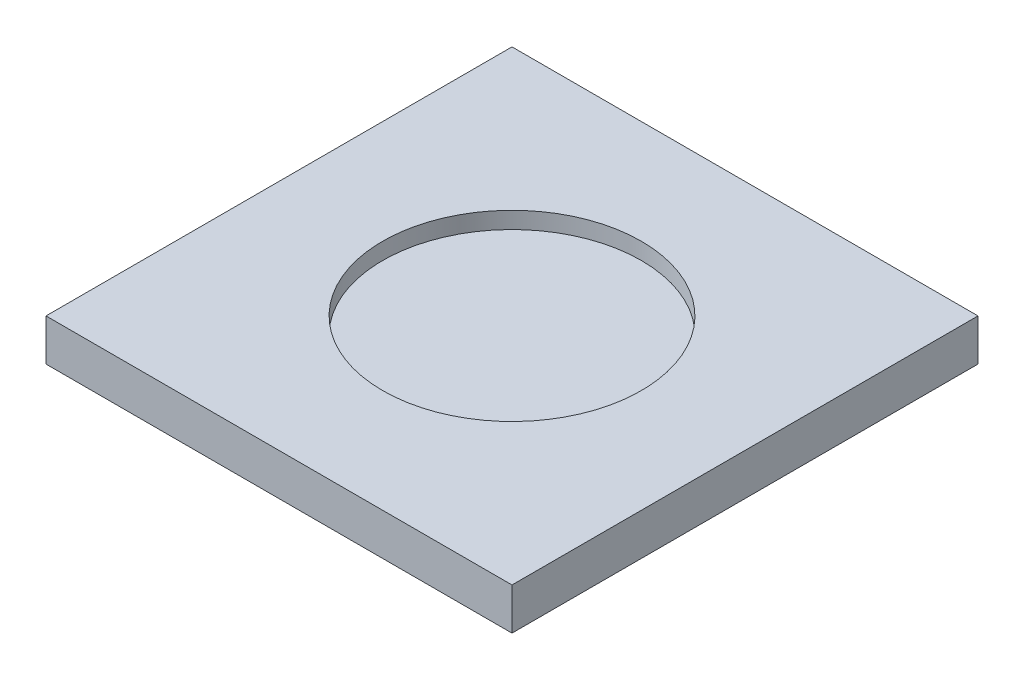
SolidWorks part; units mm, degrees
ref_plane "Front Plane" through (0, 0, 0) normal (0, 0, 1) x (1, 0, 0)
ref_plane "Top Plane" through (0, 0, 0) normal (0, 1, 0) x (1, 0, 0)
ref_plane "Right Plane" through (0, 0, 0) normal (1, 0, 0) x (0, 0, -1)
sketch "Sketch1" plane through (0, 0, 0) normal (0, 1, 0) x (1, 0, 0)
  line L1 (-44.1493, -28.699) -> (11.6841, -28.699)
  line L2 (-44.1493, -28.699) -> (-44.1493, 27.1343)
  line L3 (-44.1493, 27.1343) -> (11.6841, 27.1343)
  line L4 (11.6841, -28.699) -> (11.6841, 27.1343)
  dimension "D1" = 55.8333
  dimension "D2" = 55.8333
extrude "Boss-Extrude1" add sketch "Sketch1" along normal blind 5
sketch "Sketch2" plane through (0, 5, 0) normal (0, 1, 0) x (1, 0, 0)
  line L0 (-16.2326, 27.1343) -> (-16.2326, -28.699) construction
  line L1 (11.6841, 27.1343) -> (-44.1493, 27.1343) construction
  line L2 (-44.1493, -28.699) -> (11.6841, -28.699) construction
  circle A0 centre (-16.2326, -0.7823) radius 15.5
  dimension "D1" = 31
extrude "Cut-Extrude1" cut sketch "Sketch2" against normal blind 2
